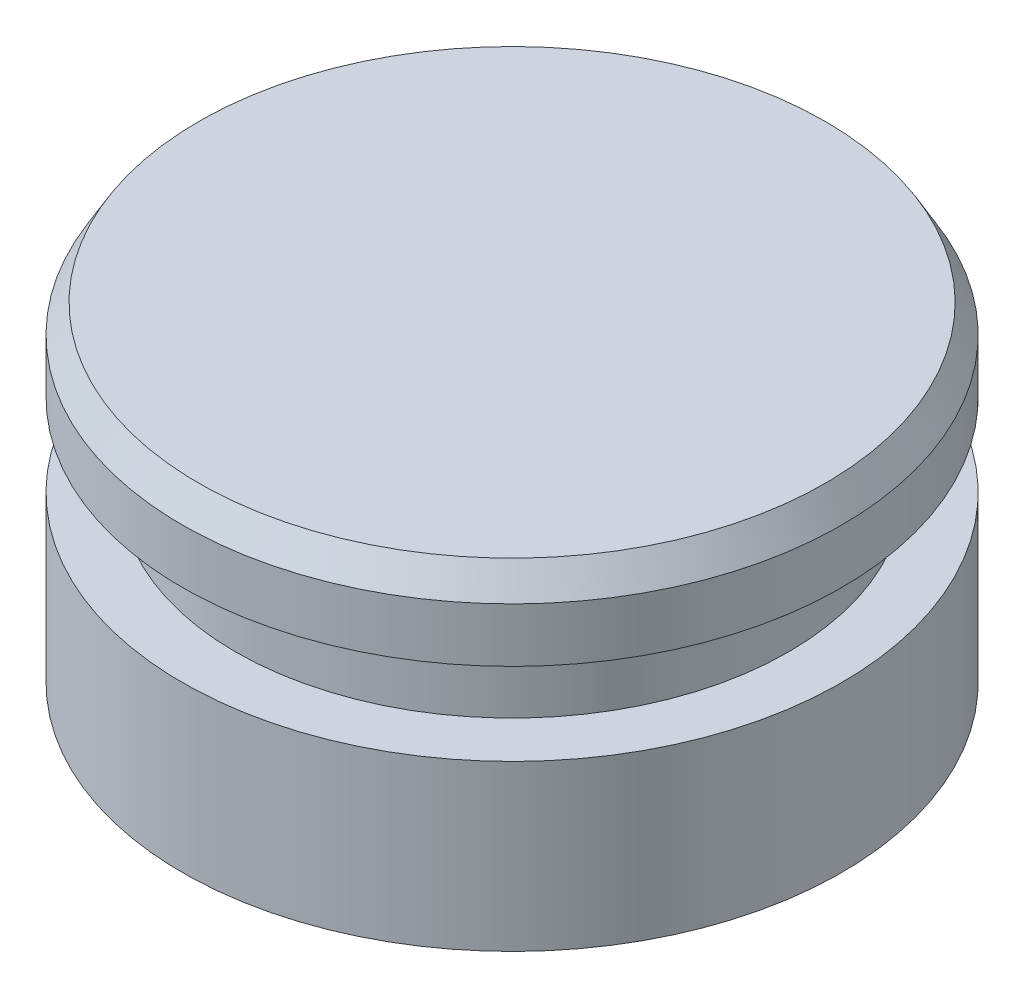
SolidWorks part; units mm, degrees
ref_plane "Front Plane" through (0, 0, 0) normal (0, 0, 1) x (1, 0, 0)
ref_plane "Top Plane" through (0, 0, 0) normal (0, 1, 0) x (1, 0, 0)
ref_plane "Right Plane" through (0, 0, 0) normal (1, 0, 0) x (0, 0, -1)
sketch "Sketch1" plane through (0, 0, 0) normal (0, 0, 1) x (1, 0, 0)
  line L0 (0, 0) -> (0, 9.525) construction
  line L1 (0, 0) -> (-9.5377, 0)
  line L4 (-8.001, 4.7625) -> (-8.001, 7.1437)
  line L5 (-8.001, 7.1437) -> (-9.5377, 7.1437)
  line L6 (-9.5377, 7.1437) -> (-9.5377, 9.525)
  line L7 (-9.5377, 9.525) -> (0, 9.525)
  line L9 (0, 0) -> (0, 9.525)
  line L11 (-8.001, 4.7625) -> (-9.5377, 4.7625)
  line L12 (-9.5377, 4.7625) -> (-9.5377, 0)
  point P5 (0, 0)
  dimension "D1" = 9.525
  dimension "D2" = 9.5377
  dimension "D3" = 2.3813
  dimension "D6" = 8.001
  dimension "D7" = 7.1437
revolve "Revolve1" add sketch "Sketch1" angle 360 about L9
chamfer "Chamfer1" distance 0.4704 angle 60 1 edges at (0, 9.525, -9.5377)
